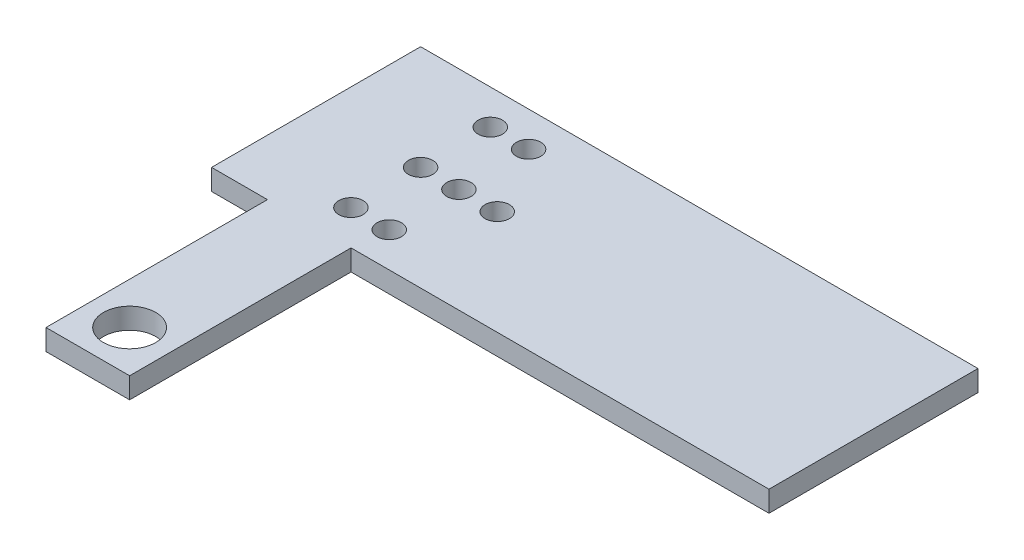
SolidWorks part; units mm, degrees
ref_plane "Front Plane" through (0, 0, 0) normal (0, 0, 1) x (1, 0, 0)
ref_plane "Top Plane" through (0, 0, 0) normal (0, 1, 0) x (1, 0, 0)
ref_plane "Right Plane" through (0, 0, 0) normal (1, 0, 0) x (0, 0, -1)
sketch "Sketch1" plane through (0, 0, 0) normal (0, 1, 0) x (1, 0, 0)
  line L1 (-40, -15) -> (40, -15)
  line L2 (-40, -15) -> (-40, 15)
  line L3 (-40, 15) -> (40, 15)
  line L4 (40, -15) -> (40, 15)
  line L5 (0, 15) -> (0, -15) construction
  line L6 (-40, 0) -> (40, 0) construction
  point P0 (0, 0)
  dimension "D1" = 30
  dimension "D2" = 80
extrude "Boss-Extrude1" add sketch "Sketch1" along normal blind 3
sketch "Sketch2" plane through (0, 3, 0) normal (0, 1, 0) x (1, 0, 0)
  line L0 (-40, 0) -> (0, 0) construction
  line L1 (-40, 15) -> (-40, -15) construction
  circle A0 centre (-25, 0) radius 1.75
  dimension "D1" = 3.5
  dimension "D2" = 15
extrude "Cut-Extrude1" cut sketch "Sketch2" against normal blind 3
pattern_linear "LPattern1" count 3 spacing 5.5 along (1, 0, 0) of "Cut-Extrude1"
sketch "Sketch3" plane through (0, 3, 0) normal (0, 1, 0) x (1, 0, 0)
  line L0 (-40, -10) -> (-6.1351, -10) construction
  line L1 (-40, 15) -> (-40, -15) construction
  line L2 (-40, -15) -> (40, -15) construction
  circle A0 centre (-25, -10) radius 1.75
  circle A1 centre (-19.5, -10) radius 1.75
  dimension "D1" = 3.5
  dimension "D2" = 5.5
  dimension "D3" = 15
  dimension "D4" = 5
extrude "Cut-Extrude2" cut sketch "Sketch3" against normal blind 3
mirror "Mirror1" about plane through (0, 0, 0) normal (0, 0, 1) of "Cut-Extrude2"
sketch "Sketch4" plane through (0, 0, 0) normal (0, 1, 0) x (1, 0, 0)
  line L0 (-45, 0) -> (-25.9822, -40.7839) construction
  line L1 (-45, 0) -> (40, 0) construction
  line L2 (40, -15) -> (40, 15) construction
  line L3 (-25.9822, -40.7839) -> (-25.9822, 15) construction
  line L4 (40, 15) -> (-40, 15) construction
  line L9 (-25.9822, -41.3119) -> (-25.9822, -14.799) construction
  line L10 (-40, -15) -> (40, -15) construction
  line L12 (-31.9822, -15) -> (-19.9822, -15)
  line L13 (-31.9822, -15) -> (-31.9822, -46.7839)
  line L14 (-31.9822, -46.7839) -> (-19.9822, -46.7839)
  line L15 (-19.9822, -15) -> (-19.9822, -46.7839)
  line L16 (-25.9822, -46.7839) -> (-25.9822, -15) construction
  line L17 (-31.9822, -30.8919) -> (-19.9822, -30.8919) construction
  circle A0 centre (-45, 0) radius 5.8635 construction
  circle A1 centre (-25, 0) radius 1.75 construction
  circle A2 centre (-25.9822, -40.7839) radius 3.75
  point P9 (-25.9822, -30.8919)
  point P13 (-25.9822, -28.0554)
  dimension "D1" = 20
  dimension "D6" = 7.5
  dimension "D2" = 45
  dimension "D3" = 65
  dimension "D4" = 12
  dimension "D5" = 6
extrude "Boss-Extrude2" add sketch "Sketch4" along normal blind 3
